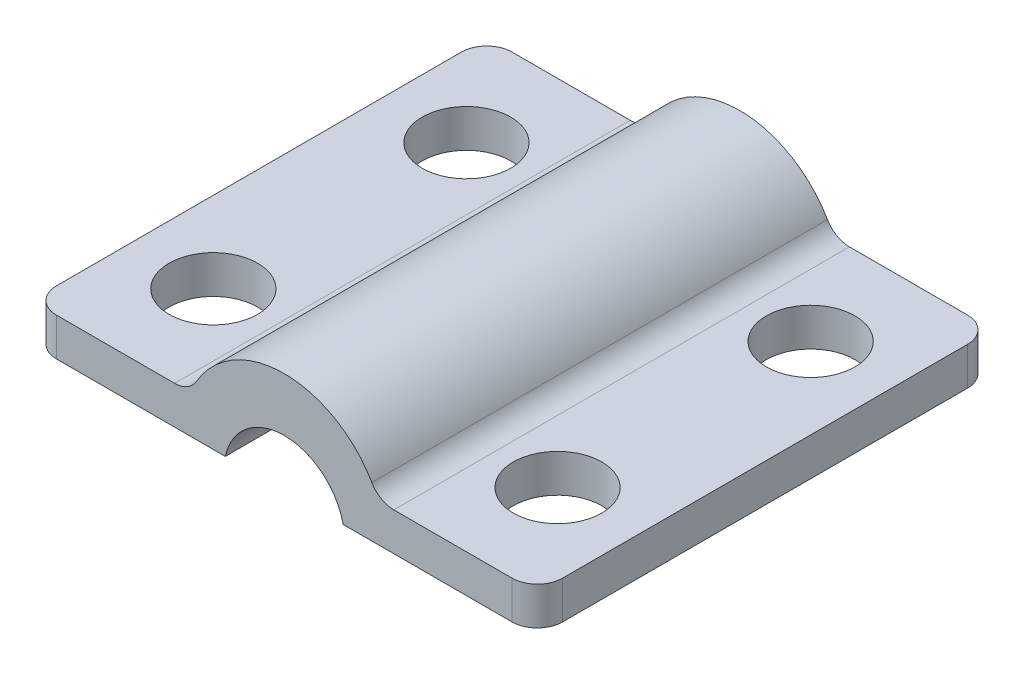
SolidWorks part; units mm, degrees
ref_plane "Front Plane" through (0, 0, 0) normal (0, 0, 1) x (1, 0, 0)
ref_plane "Top Plane" through (0, 0, 0) normal (0, 1, 0) x (1, 0, 0)
ref_plane "Right Plane" through (0, 0, 0) normal (1, 0, 0) x (0, 0, -1)
sketch "Sketch1" plane through (0, 0, 0) normal (0, 0, 1) x (1, 0, 0)
  line L0 (-10, 0) -> (10, 0)
  line L1 (-10, 1.5) -> (10, 1.5)
  line L2 (-10, 1.5) -> (-10, -1.5)
  line L3 (-10, -1.5) -> (10, -1.5)
  line L4 (10, 1.5) -> (10, -1.5)
  line L5 (-10, 1.5) -> (10, -1.5) construction
  line L6 (-10, -1.5) -> (10, 1.5) construction
  circle A0 centre (0, 0) radius 4
  dimension "D1" = 8
  dimension "D2" = 3
  dimension "D3" = 20
extrude "Boss-Extrude1" add sketch "Sketch1" against normal mid plane 18 contours A0 L1 L2 L0 | L0 A0 L1 | A0 L0 L4 L1 | L1 A0
sketch "Sketch3" plane through (0, 0, 9) normal (0, 0, 1) x (1, 0, 0)
  line L0 (0, -0.5) -> (0, 0) construction
  circle A0 centre (0, -0.5) radius 2.3813
  dimension "D2" = 4.7625
  dimension "D1" = 0.5
extrude "Cut-Extrude1" cut sketch "Sketch3" against normal up to next
sketch "Sketch4" plane through (0, 1.5, 0) normal (0, 1, 0) x (1, 0, 0)
  line L0 (0, 9) -> (0, -9) construction
  line L1 (3.7081, 9) -> (-3.7081, 9) construction
  line L2 (-3.7081, -9) -> (3.7081, -9) construction
  line L9 (-10, 0) -> (10, 0) construction
  line L10 (-10, 9) -> (-10, -9) construction
  line L11 (10, 9) -> (10, -9) construction
  circle A0 centre (-6.8, 5) radius 1.75
  circle A1 centre (6.8, 5) radius 1.75
  circle A2 centre (6.8, -5) radius 1.75
  circle A3 centre (-6.8, -5) radius 1.75
  dimension "D2" = 3.5
  dimension "D3" = 3.5
  dimension "D1" = 5
  dimension "D4" = 5
  dimension "D5" = 6.8
  dimension "D6" = 6.8
extrude "Cut-Extrude2" cut sketch "Sketch4" against normal up to next
fillet "Fillet1" radius 1 4 edges at (10, 0.75, 9) (10, 0.75, -9) (-10, 0.75, -9) (-10, 0.75, 9)
fillet "Fillet2" radius 1 2 edges at (3.7081, 1.5, 0) (-3.7081, 1.5, 0)
